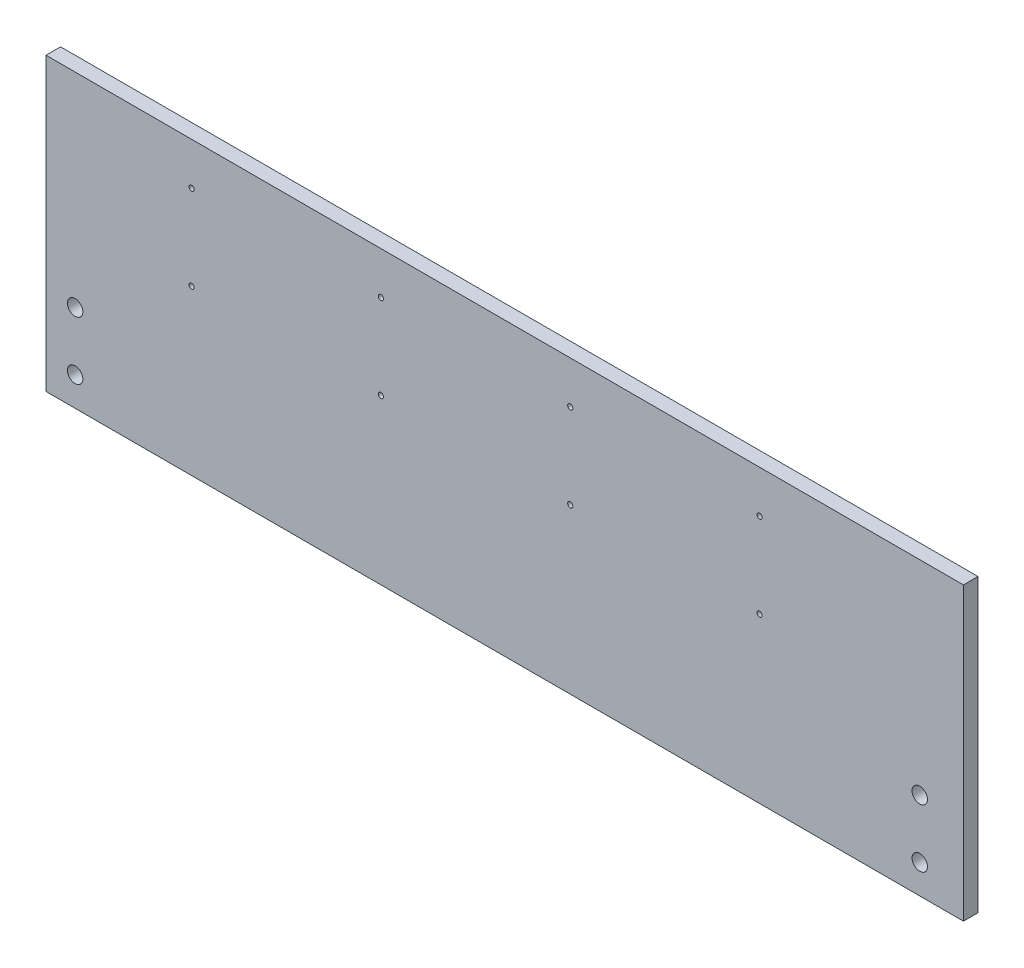
SolidWorks part; units mm, degrees
ref_plane "Front Plane" through (0, 0, 0) normal (0, 0, 1) x (1, 0, 0)
ref_plane "Top Plane" through (0, 0, 0) normal (0, 1, 0) x (1, 0, 0)
ref_plane "Right Plane" through (0, 0, 0) normal (1, 0, 0) x (0, 0, -1)
sketch "Sketch1" plane through (0, 0, 0) normal (0, 0, 1) x (1, 0, 0)
  line L1 (-200.025, -63.5) -> (200.025, -63.5)
  line L2 (-200.025, -63.5) -> (-200.025, 63.5)
  line L3 (-200.025, 63.5) -> (200.025, 63.5)
  line L4 (200.025, -63.5) -> (200.025, 63.5)
  line L5 (-200.025, -63.5) -> (200.025, 63.5) construction
  line L6 (-200.025, 63.5) -> (200.025, -63.5) construction
  point P0 (0, 0)
  dimension "D1" = 127
  dimension "D2" = 400.05
extrude "Boss-Extrude1" add sketch "Sketch1" along normal blind 6.35
sketch "Sketch2" plane through (0, 0, 0) normal (0, 0, -1) x (-1, 0, 0)
  line L0 (200.025, -63.5) -> (-200.025, -63.5) construction
  line L1 (-200.025, -63.5) -> (-200.025, 63.5) construction
  line L2 (200.025, 63.5) -> (200.025, -63.5) construction
  line L3 (-200.025, -63.5) -> (-200.025, 63.5) construction
  line L4 (200.025, 63.5) -> (200.025, -63.5) construction
  circle A0 centre (-180.975, -50.8) radius 3.3655
  circle A1 centre (-180.975, -25.4) radius 3.3655
  circle A2 centre (187.325, -50.8) radius 3.3655
  circle A3 centre (187.325, -25.4) radius 3.3655
  dimension "D1" = 6.731
  dimension "D2" = 6.731
  dimension "D7" = 6.731
  dimension "D9" = 6.731
  dimension "D3" = 12.7
  dimension "D4" = 19.05
  dimension "D5" = 25.4
  dimension "D6" = 25.4
  dimension "D8" = 12.7
  dimension "D10" = 19.05
  dimension "D11" = 12.7
extrude "Cut-Extrude1" cut sketch "Sketch2" against normal through all
sketch "Sketch3" plane through (0, 0, 6.35) normal (0, 0, 1) x (1, 0, 0)
  circle A0 centre (-136.525, 8.025) radius 1.6 construction
  circle A1 centre (-136.525, 45.025) radius 1.6 construction
  circle A2 centre (-53.975, 8.025) radius 1.6 construction
  circle A3 centre (-53.975, 45.025) radius 1.6 construction
  circle A4 centre (28.575, 8.025) radius 1.6 construction
  circle A5 centre (28.575, 45.025) radius 1.6 construction
  circle A6 centre (111.125, 8.025) radius 1.6 construction
  circle A7 centre (111.125, 45.025) radius 1.6 construction
  circle A8 centre (-136.525, 8.025) radius 1.6
  circle A9 centre (-136.525, 45.025) radius 1.6
  circle A10 centre (-53.975, 8.025) radius 1.6
  circle A11 centre (-53.975, 45.025) radius 1.6
  circle A12 centre (28.575, 8.025) radius 1.6
  circle A13 centre (28.575, 45.025) radius 1.6
  circle A14 centre (111.125, 8.025) radius 1.6
  circle A15 centre (111.125, 45.025) radius 1.6
hole_wizard "#4-40 Tapped Hole1" positions "Sketch4" profile "Sketch6" tap size "#4-40" standard "ANSI Inch" end condition through all
sketch "Sketch4" plane through (0, 0, 6.35) normal (0, 0, 1) x (1, 0, 0)
  point P0 (-136.525, 45.025)
  point P4 (-136.525, 8.025)
  point P7 (-53.975, 45.025)
  point P10 (-53.975, 8.025)
  point P13 (28.575, 45.025)
  point P16 (28.575, 8.025)
  point P19 (111.125, 45.025)
  point P22 (111.125, 8.025)
sketch "Sketch6" plane through (-136.525, 45.025, 6.35) normal (1, 0, 0) x (0, -1, 0)
  line L0 (0, 0) -> (0, 6.35)
  line L1 (0, 6.35) -> (1.1303, 6.35)
  line L2 (1.1303, 6.35) -> (1.1303, 0)
  line L5 (1.1303, 0) -> (0, 0)
  line L11 (0, -6.35) -> (0, 107.95) construction
  dimension "Thru Tap Drill Dia." = 2.2606
  dimension "Thru Tap Drill Depth" = 6.35
cosmetic thread "Hole Thread1" parameters "D2"=2.8448
cosmetic thread "Hole Thread2" parameters "D2"=2.8448
cosmetic thread "Hole Thread3" parameters "D2"=2.8448
cosmetic thread "Hole Thread4" parameters "D2"=2.8448
cosmetic thread "Hole Thread5" parameters "D2"=2.8448
cosmetic thread "Hole Thread6" parameters "D2"=2.8448
cosmetic thread "Hole Thread7" parameters "D2"=2.8448
cosmetic thread "Hole Thread8" parameters "D2"=2.8448
